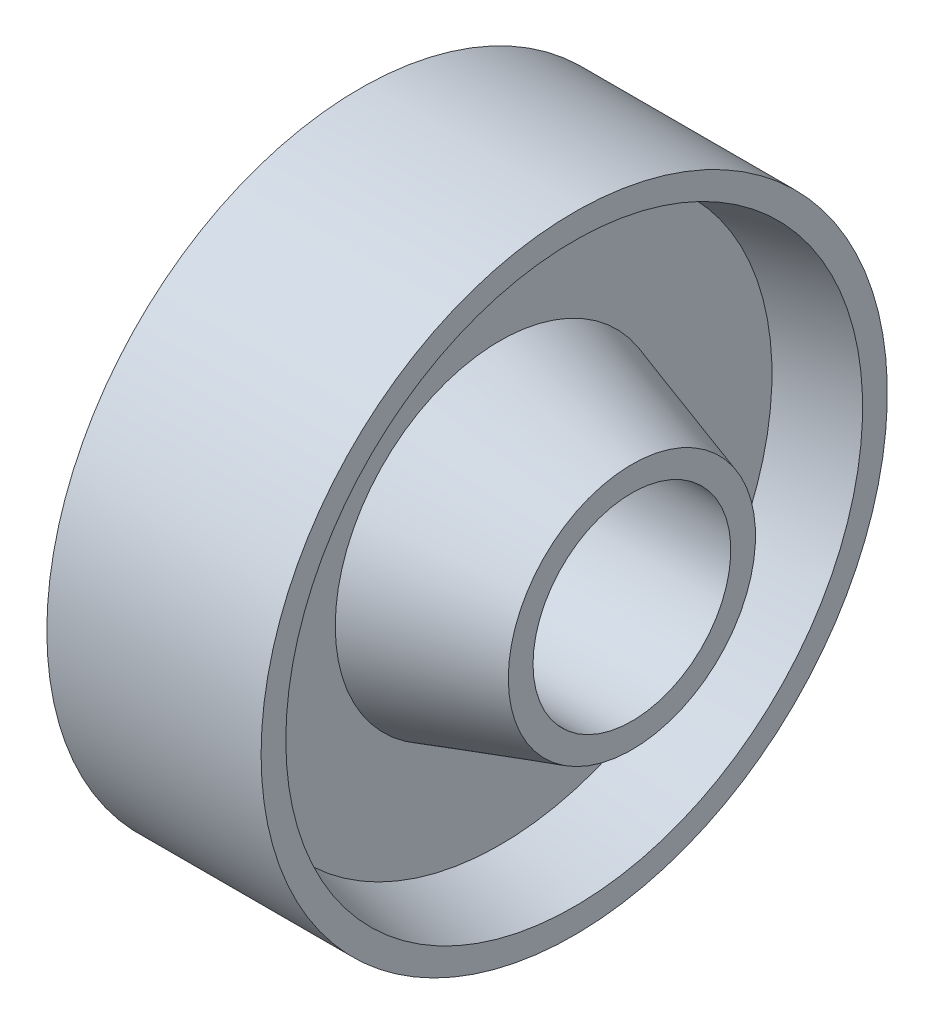
SolidWorks part; units mm, degrees
ref_plane "Front Plane" through (0, 0, 0) normal (0, 0, 1) x (1, 0, 0)
ref_plane "Top Plane" through (0, 0, 0) normal (0, 1, 0) x (1, 0, 0)
ref_plane "Right Plane" through (0, 0, 0) normal (1, 0, 0) x (0, 0, -1)
sketch "Sketch1" plane through (0, 0, 0) normal (0, 1, 0) x (1, 0, 0)
  line L0 (0, 0) -> (135.24, 0) construction
  line L2 (26.1965, 12) -> (66.1965, 12)
  line L4 (26.1965, 12) -> (26.1965, 15)
  line L5 (66.1965, 12) -> (66.1965, 15)
  line L7 (50.1965, 20) -> (50.1965, 33)
  line L8 (42.1965, 20) -> (42.1965, 33)
  line L11 (26.1965, 15) -> (42.1965, 20)
  line L12 (50.1965, 20) -> (66.1965, 15)
  line L13 (33.1965, 38) -> (59.1965, 38)
  line L15 (59.1965, 38) -> (59.1965, 35)
  line L16 (33.1965, 38) -> (33.1965, 35)
  line L17 (33.1965, 35) -> (42.1965, 33)
  line L18 (50.1965, 33) -> (59.1965, 35)
revolve "Revolve3" add sketch "Sketch1" angle 360 about L0
